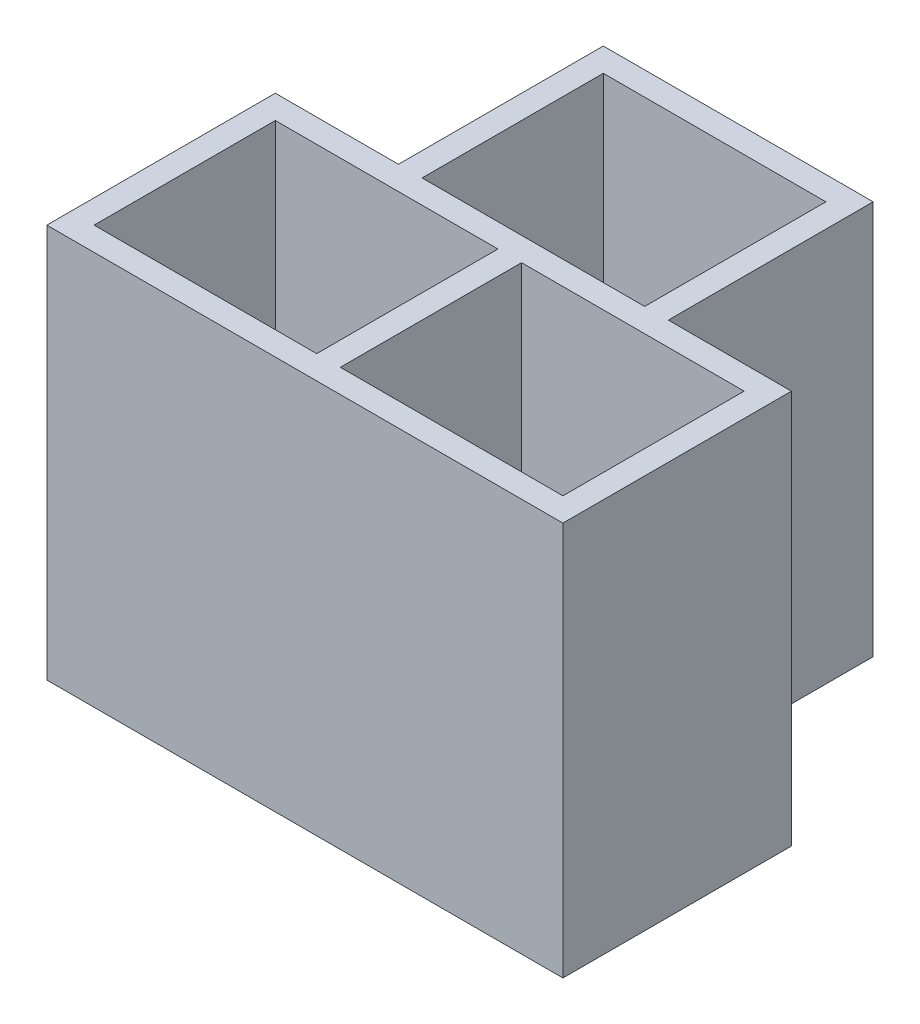
SolidWorks part; units mm, degrees
ref_plane "Plano frontal" through (0, 0, 0) normal (0, 0, 1) x (1, 0, 0)
ref_plane "Plano superior" through (0, 0, 0) normal (0, 1, 0) x (1, 0, 0)
ref_plane "Plano direito" through (0, 0, 0) normal (1, 0, 0) x (0, 0, -1)
sketch "Sketch1" plane through (0, 0, 0) normal (0, 1, 0) x (1, 0, 0)
  line L1 (-6.55, 2.9) -> (6.55, 2.9)
  line L2 (-6.55, 2.9) -> (-6.55, -2.9)
  line L3 (-6.55, -2.9) -> (6.55, -2.9)
  line L4 (6.55, 2.9) -> (6.55, -2.9)
  point P4 (0, 2.9)
  point P6 (-6.55, 0)
  dimension "D1" = 13.1
  dimension "D2" = 5.8
extrude "Boss-Extrude1" add sketch "Sketch1" along normal mid plane 10
sketch "Sketch10" plane through (0, 5, 0) normal (0, 1, 0) x (1, 0, 0)
  line L0 (6.55, 2.9) -> (-6.55, 2.9) construction
  line L1 (-5.95, 2.3) -> (-0.3, 2.3)
  line L2 (-5.95, 2.3) -> (-5.95, -2.3)
  line L3 (-5.95, -2.3) -> (-0.3, -2.3)
  line L4 (5.95, 2.3) -> (5.95, -2.3)
  line L5 (-6.55, 2.9) -> (-6.55, -2.9) construction
  line L6 (-0.3, 2.3) -> (-0.3, -2.3)
  line L7 (0, -3.19) -> (0, 3.19) construction
  line L8 (0.3, 2.3) -> (0.3, -2.3)
  line L9 (0.3, 2.3) -> (5.95, 2.3)
  line L10 (-0.3, 2.3) -> (0.3, 2.3) construction
  line L11 (0.3, -2.3) -> (5.95, -2.3)
  line L12 (-0.3, -2.3) -> (0.3, -2.3) construction
  point P6 (-5.95, 0)
  dimension "D1" = 0.6
  dimension "D2" = 0.6
  dimension "D3" = 0.6
extrude "Cut-Extrude7" cut sketch "Sketch10" against normal offset from surface (6.6 mm away) 3.4 up to face at (0, -5, 0)
sketch "Sketch9" plane through (0, 0, 0) normal (0, 1, 0) x (1, 0, 0)
  line L0 (-5.95, 2.3) -> (-0.3, 2.3) construction
  line L1 (-3.125, 2.3) -> (-3.125, -2.3) construction
  line L4 (-5.95, 2.3) -> (-0.3, 2.3) construction
  line L6 (-5.95, -2.3) -> (-5.95, 2.3) construction
  line L8 (-0.3, -2.3) -> (-5.95, -2.3) construction
  line L11 (0, -3.19) -> (0, 3.19) construction
  circle A0 centre (-4.625, 0) radius 0.75
  circle A2 centre (-1.625, 0) radius 0.75
  circle A3 centre (1.625, 0) radius 0.75
  circle A4 centre (4.625, 0) radius 0.75
  point P17 (-3.125, 0)
  dimension "D1" = 1.5
  dimension "D2" = 1.5
  dimension "D3" = 0.575
extrude "Cut-Extrude6" cut sketch "Sketch9" against normal through all both and the other way through all
sketch "Sketch11" plane through (0, 0, 0) normal (0, 1, 0) x (1, 0, 0)
  line L0 (6.55, 2.9) -> (-6.55, 2.9) construction
  line L1 (-3.425, 2.9) -> (3.425, 2.9)
  line L2 (-2.825, 2.9) -> (-2.825, 7.5)
  line L3 (-2.825, 7.5) -> (2.825, 7.5)
  line L4 (2.825, 2.9) -> (2.825, 7.5)
  line L5 (-0.3, 2.3) -> (-5.95, 2.3) construction
  line L6 (-5.95, 2.3) -> (-5.95, -2.3) construction
  line L7 (-3.425, 2.9) -> (-3.425, 8.1)
  line L8 (-3.425, 8.1) -> (3.425, 8.1)
  line L9 (3.425, 2.9) -> (3.425, 8.1)
  line L11 (-3.425, 2.3) -> (3.425, 2.3) construction
  line L12 (-2.825, 2.9) -> (2.825, 2.9) construction
  line L14 (-3.425, 2.3) -> (-3.425, 8.1) construction
  line L15 (3.425, 2.3) -> (3.425, 8.1) construction
  point P17 (0, 2.9)
  dimension "D1" = 0.6
extrude "Boss-Extrude2" add sketch "Sketch11" along normal up to surface and the other way up to surface contours L1 L9 L8 L7 L2 L3 L4
sketch "Sketch12" plane through (0, -5, 0) normal (0, -1, 0) x (1, 0, 0)
  line L0 (0, -5.5) -> (0, 5.5) construction
  line L1 (-2.825, -2.9) -> (2.825, -2.9)
  line L2 (-2.825, -2.9) -> (-2.825, -7.5)
  line L3 (-2.825, -7.5) -> (2.825, -7.5)
  line L4 (2.825, -2.9) -> (2.825, -7.5)
  line L5 (-4.625, 0) -> (-1.625, 0) construction
  circle A0 centre (-1.5, -5.2) radius 0.75
  circle A1 centre (-1.625, 0) radius 0.75 construction
  circle A2 centre (1.5, -5.2) radius 0.75
  point P9 (-2.825, -5.2)
  dimension "D1" = 3
  dimension "D2" = 3
extrude "Boss-Extrude3" add sketch "Sketch12" against normal up to surface (3.4 mm away) up to face at (-4.625, -1.6, 0.75)
